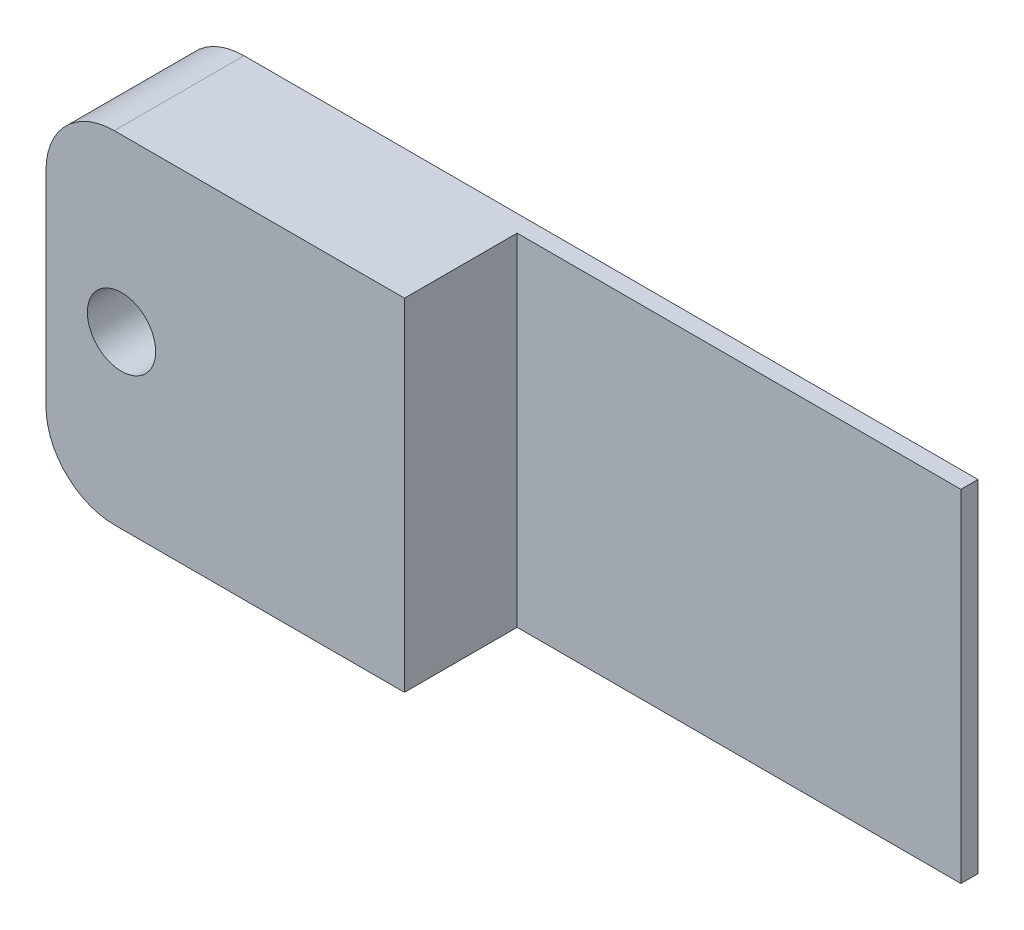
SolidWorks part; units mm, degrees
ref_plane "Спереди" through (0, 0, 0) normal (0, 0, 1) x (1, 0, 0)
ref_plane "Сверху" through (0, 0, 0) normal (0, 1, 0) x (1, 0, 0)
ref_plane "Справа" through (0, 0, 0) normal (1, 0, 0) x (0, 0, -1)
sketch "Эскиз1" plane through (0, 0, 0) normal (0, 0, 1) x (1, 0, 0)
  line L1 (-9.75, 5) -> (11.75, 5)
  line L2 (-11.75, 3) -> (-11.75, -3)
  line L3 (-9.75, -5) -> (11.75, -5)
  line L4 (11.75, 5) -> (11.75, -5)
  line L5 (-11.75, 5) -> (11.75, -5) construction
  line L6 (-11.75, -5) -> (11.75, 5) construction
  circle A0 centre (-9.5385, 0) radius 1
  arc A1 (-11.75, -3) -> (-9.75, -5) centre (-9.75, -3) ccw
  arc A2 (-9.75, 5) -> (-11.75, 3) centre (-9.75, 3) ccw
  point P0 (0, 0)
  dimension "D3" = 2
  dimension "D1" = 10
  dimension "D2" = 23.5
extrude "Бобышка-Вытянуть1" add sketch "Эскиз1" along normal blind 3.8
sketch "Эскиз2" plane through (0, 0, 3.8) normal (0, 0, 1) x (1, 0, 0)
  line L0 (-9.75, -5) -> (11.75, -5) construction
  line L1 (11.75, 5) -> (-1.25, 5)
  line L2 (11.75, 5) -> (11.75, -5)
  line L3 (11.75, -5) -> (-1.25, -5)
  line L4 (-1.25, 5) -> (-1.25, -5)
  dimension "D1" = 13
extrude "Вырез-Вытянуть1" cut sketch "Эскиз2" against normal blind 3.3
